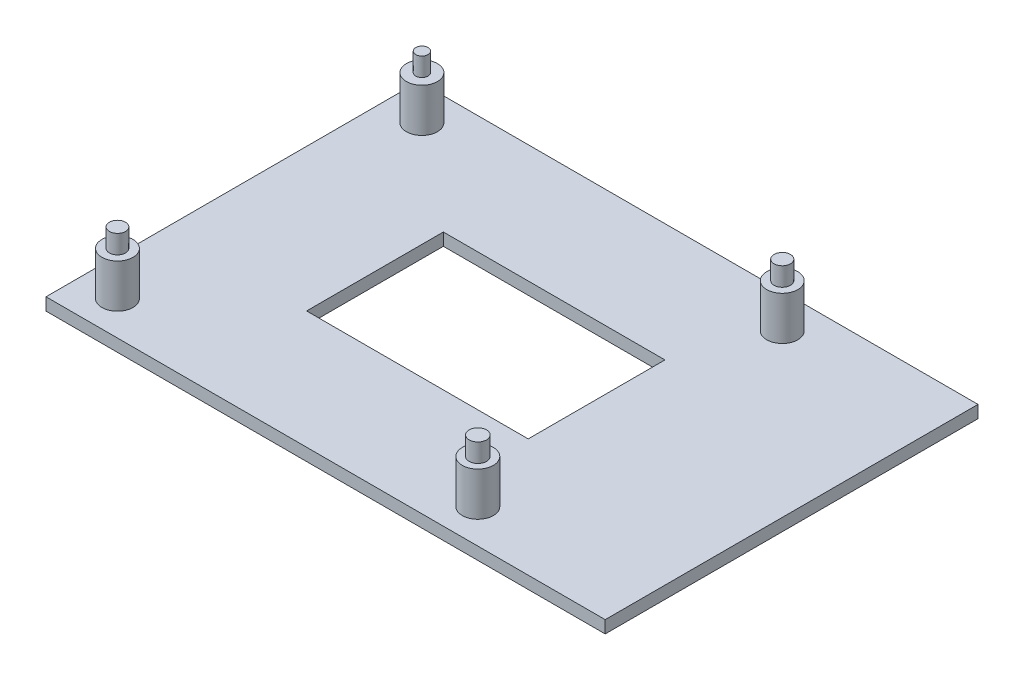
SolidWorks part; units mm, degrees
ref_plane "Alzado" through (0, 0, 0) normal (0, 0, 1) x (1, 0, 0)
ref_plane "Planta" through (0, 0, 0) normal (0, 1, 0) x (1, 0, 0)
ref_plane "Vista lateral" through (0, 0, 0) normal (1, 0, 0) x (0, 0, -1)
sketch "Croquis1" plane through (0, 0, 0) normal (0, 1, 0) x (1, 0, 0)
  line L1 (-45, 30) -> (45, 30)
  line L2 (-45, 30) -> (-45, -30)
  line L3 (-45, -30) -> (45, -30)
  line L4 (45, 30) -> (45, -30)
  line L5 (-45, 30) -> (45, -30) construction
  line L6 (-45, -30) -> (45, 30) construction
  point P0 (0, 0)
  point P6 (0, 0)
  dimension "D1" = 90
  dimension "D2" = 60
extrude "Saliente-Extruir1" add sketch "Croquis1" along normal blind 2
sketch "Croquis2" plane through (0, 2, 0) normal (0, 1, 0) x (1, 0, 0)
  line L0 (0, 30) -> (0, -30) construction
  line L1 (-39, 24.5) -> (19, 24.5) construction
  line L2 (-39, 24.5) -> (-39, -24.5) construction
  line L3 (-39, -24.5) -> (19, -24.5) construction
  line L4 (19, 24.5) -> (19, -24.5) construction
  line L5 (-39, 24.5) -> (19, -24.5) construction
  line L6 (-39, -24.5) -> (19, 24.5) construction
  line L7 (-42.5, 28) -> (42.5, 28) construction
  line L8 (-42.5, 28) -> (-42.5, -28) construction
  line L9 (-42.5, -28) -> (42.5, -28) construction
  line L10 (42.5, 28) -> (42.5, -28) construction
  line L11 (-45, -30) -> (45, -30) construction
  line L12 (45, 30) -> (-45, 30) construction
  circle A0 centre (-39, 24.5) radius 2.5
  circle A1 centre (19, 24.5) radius 2.5
  circle A2 centre (19, -24.5) radius 2.5
  circle A3 centre (-39, -24.5) radius 2.5
  point P0 (-10, 0)
  point P5 (-10, 0)
  dimension "D6" = 5
  dimension "D1" = 58
  dimension "D2" = 49
  dimension "D3" = 3.5
  dimension "D4" = 3.5
  dimension "D5" = 23.5
extrude "Saliente-Extruir2" add sketch "Croquis2" along normal blind 7
sketch "Croquis3" plane through (0, 9, 0) normal (0, 1, 0) x (1, 0, 0)
  circle A0 centre (-39, 24.5) radius 0.9873
  circle A1 centre (19, 24.5) radius 1.3168
  circle A2 centre (19, -24.5) radius 1.3995
  circle A3 centre (-39, -24.5) radius 1.2947
extrude "Saliente-Extruir3" add sketch "Croquis3" along normal blind 3
sketch "Croquis4" plane through (0, 2, 0) normal (0, 1, 0) x (1, 0, 0)
  line L1 (-22.0537, 11.0057) -> (13.6128, 11.0057)
  line L2 (-22.0537, 11.0057) -> (-22.0537, -11.0057)
  line L3 (-22.0537, -11.0057) -> (13.6128, -11.0057)
  line L4 (13.6128, 11.0057) -> (13.6128, -11.0057)
  line L5 (-22.0537, 11.0057) -> (13.6128, -11.0057) construction
  line L6 (-22.0537, -11.0057) -> (13.6128, 11.0057) construction
  point P0 (-4.2205, 0)
extrude "Cortar-Extruir1" cut sketch "Croquis4" against normal blind 3
